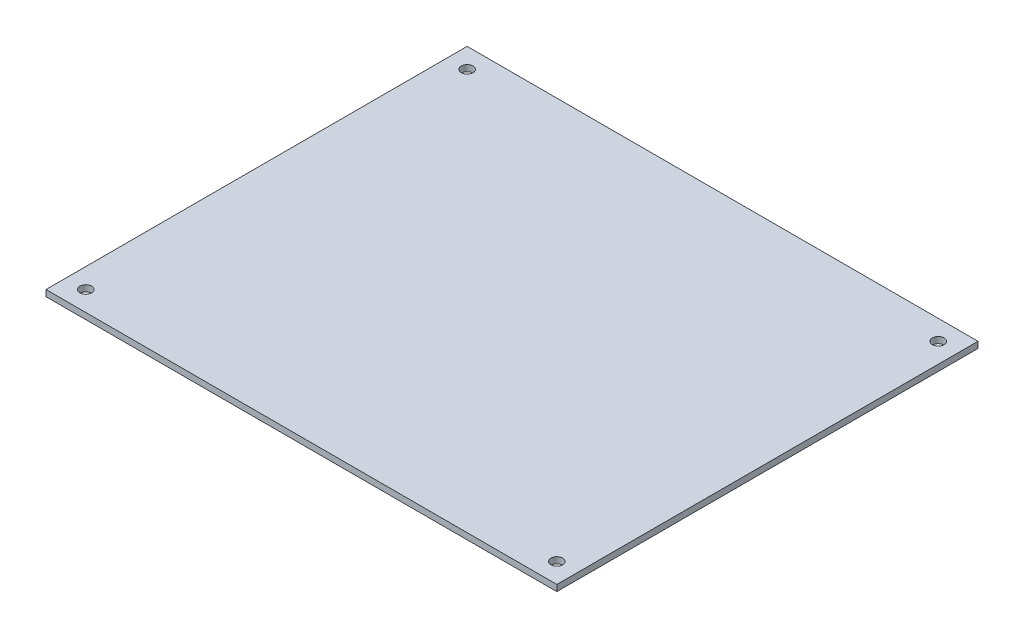
SolidWorks part; units mm, degrees
ref_plane "Plano frontal" through (0, 0, 0) normal (0, 0, 1) x (1, 0, 0)
ref_plane "Plano superior" through (0, 0, 0) normal (0, 1, 0) x (1, 0, 0)
ref_plane "Plano direito" through (0, 0, 0) normal (1, 0, 0) x (0, 0, -1)
sketch "Esboço1" plane through (0, 0, 0) normal (0, 1, 0) x (1, 0, 0)
  line L1 (-65.5, 54) -> (65.5, 54)
  line L2 (-65.5, 54) -> (-65.5, -54)
  line L3 (-65.5, -54) -> (65.5, -54)
  line L4 (65.5, 54) -> (65.5, -54)
  line L5 (-65.5, 54) -> (65.5, -54) construction
  line L6 (-65.5, -54) -> (65.5, 54) construction
  circle A0 centre (-60.4, 48.9) radius 1.5
  circle A1 centre (-60.4, -48.9) radius 1.5
  circle A2 centre (60.4, -48.9) radius 1.5
  circle A3 centre (60.4, 48.9) radius 1.5
  point P0 (0, 0)
  dimension "D3" = 5.1
  dimension "D4" = 5.1
  dimension "D5" = 5.1
  dimension "D6" = 5.1
  dimension "D7" = 5.1
  dimension "D8" = 5.1
  dimension "D9" = 5.1
  dimension "D10" = 5.1
  dimension "D11" = 3
  dimension "D1" = 108
  dimension "D2" = 131
extrude "Ressalto-extrusão1" add sketch "Esboço1" along normal blind 1.6
sketch "Esboço2"
